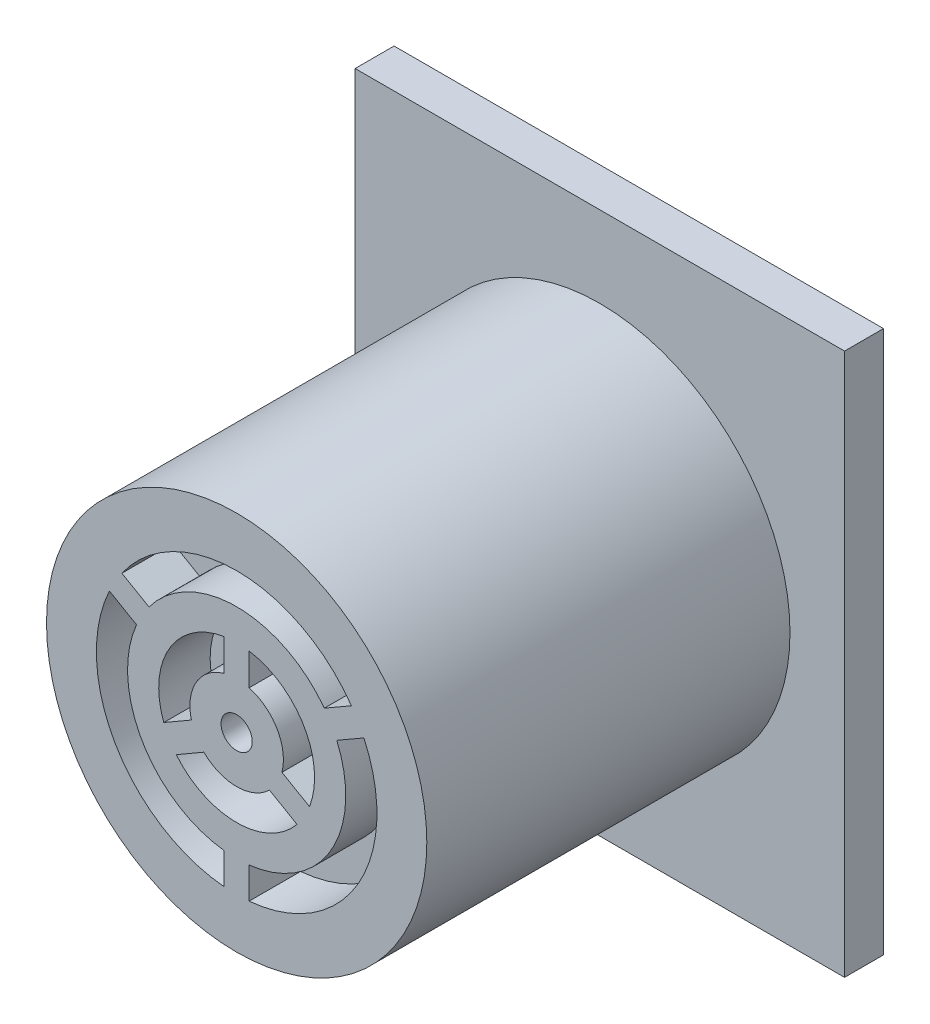
SolidWorks part; units mm, degrees
ref_plane "Front Plane" through (0, 0, 0) normal (0, 0, 1) x (1, 0, 0)
ref_plane "Top Plane" through (0, 0, 0) normal (0, 1, 0) x (1, 0, 0)
ref_plane "Right Plane" through (0, 0, 0) normal (1, 0, 0) x (0, 0, -1)
sketch "Sketch1" plane through (0, 0, 0) normal (0, 0, 1) x (1, 0, 0)
  line L1 (-9.9695, -11.049) -> (9.9695, -11.049)
  line L2 (-9.9695, -11.049) -> (-9.9695, 11.049)
  line L3 (-9.9695, 11.049) -> (9.9695, 11.049)
  line L4 (9.9695, -11.049) -> (9.9695, 11.049)
  line L5 (-9.9695, -11.049) -> (9.9695, 11.049) construction
  line L6 (-9.9695, 11.049) -> (9.9695, -11.049) construction
  point P0 (0, 0)
  dimension "D1" = 19.939
  dimension "D2" = 22.098
extrude "Extrude1" add sketch "Sketch1" along normal blind 1.5875
sketch "Sketch2" plane through (0, 0, 1.5875) normal (0, 0, 1) x (1, 0, 0)
  circle A0 centre (0, 0) radius 7.747
  dimension "D1" = 15.494
extrude "Extrude2" add sketch "Sketch2" along normal blind 14.7955 separate body
sketch "Sketch3" plane through (0, 0, 16.383) normal (0, 0, 1) x (1, 0, 0)
  line L0 (0, 1.905) -> (0, 7.747) construction
  line L1 (1.6498, -0.9525) -> (6.7091, -3.8735) construction
  line L2 (-1.6498, -0.9525) -> (-6.7091, -3.8735) construction
  line L3 (0.508, 1.836) -> (0.508, 3.1341)
  line L4 (-1.844, -0.4781) -> (-2.9682, -1.1271)
  line L5 (1.336, -1.3579) -> (2.4602, -2.007)
  line L6 (-0.508, 1.836) -> (-0.508, 3.1341)
  line L7 (-1.336, -1.3579) -> (-2.4602, -2.007)
  line L8 (1.844, -0.4781) -> (2.9682, -1.1271)
  line L9 (0, 0) -> (6.0492, 3.4925) construction
  line L10 (0.508, -4.4159) -> (0.508, -5.6924)
  line L11 (-0.508, -6.9665) -> (-0.508, -6.985)
  line L12 (0.508, -6.9665) -> (0.508, -6.985)
  line L13 (6.2872, 3.0433) -> (6.3032, 3.0526)
  line L14 (-0.508, -4.4159) -> (-0.508, -5.6924)
  line L15 (5.7792, 3.9232) -> (5.7952, 3.9324)
  line L16 (-6.2872, 3.0433) -> (-6.3032, 3.0526)
  line L19 (-4.0783, 1.768) -> (-5.1837, 2.4062)
  line L20 (-3.5703, 2.6479) -> (-4.6757, 3.2861)
  line L23 (3.5703, 2.6479) -> (4.6757, 3.2861)
  line L24 (4.0783, 1.768) -> (5.1837, 2.4062)
  line L27 (-5.7792, 3.9232) -> (-5.7952, 3.9324)
  circle A0 centre (0, 0) radius 0.635
  arc A1 (-0.508, 1.836) -> (-1.844, -0.4781) centre (0, 0) ccw
  arc A2 (-0.508, 3.1341) -> (-2.9682, -1.1271) centre (0, 0) ccw
  arc A3 (3.5703, 2.6479) -> (-3.5703, 2.6479) centre (0, 0) ccw
  arc A4 (0.508, -5.6924) -> (5.1837, 2.4062) centre (0, 0) ccw
  circle A5 centre (0, 0) radius 6.985
  circle A6 centre (0, 0) radius 7.747 construction
  circle A7 centre (0, 0) radius 1.905 construction
  arc A8 (-1.336, -1.3579) -> (1.336, -1.3579) centre (0, 0) ccw
  arc A9 (1.844, -0.4781) -> (0.508, 1.836) centre (0, 0) ccw
  circle A11 centre (0, 0) radius 3.175 construction
  arc A12 (-2.4602, -2.007) -> (2.4602, -2.007) centre (0, 0) ccw
  arc A13 (2.9682, -1.1271) -> (0.508, 3.1341) centre (0, 0) ccw
  circle A14 centre (0, 0) radius 4.445 construction
  arc A15 (-4.0783, 1.768) -> (-0.508, -4.4159) centre (0, 0) ccw
  arc A16 (0.508, -4.4159) -> (4.0783, 1.768) centre (0, 0) ccw
  circle A17 centre (0, 0) radius 5.715 construction
  arc A18 (4.6757, 3.2861) -> (-4.6757, 3.2861) centre (0, 0) ccw
  arc A19 (-5.1837, 2.4062) -> (-0.508, -5.6924) centre (0, 0) ccw
  dimension "D6" = 1.27
  dimension "D7" = 60
  dimension "D1" = 1.27
  dimension "D2" = 1.27
  dimension "D3" = 1.27
  dimension "D4" = 1.27
  dimension "D5" = 1.27
extrude "Extrude3" cut sketch "Sketch3" against normal blind 2.0955 contours L23 A18 L20 A3 | L19 A19 L14 A15 | L6 A2 L4 A1 | L7 A12 L5 A8 | A0 | L8 A13 L3 A9 | A16 L10 A4 L24
sketch "Sketch4" plane through (0, 0, 0) normal (0, 1, 0) x (1, 0, 0)
  line L0 (0, -16.383) -> (0, -397.383) construction
  line L1 (-7.747, -16.383) -> (7.747, -16.383) construction
  line L2 (0, -16.383) -> (276.8127, -397.383)
  line L3 (276.8127, -397.383) -> (0, -397.383)
  line L4 (0, -16.383) -> (0, -397.383)
  dimension "D1" = 36
  dimension "D2" = 381
revolve "Revolve1" [suppressed] add sketch "Sketch4" angle 360 about L0
